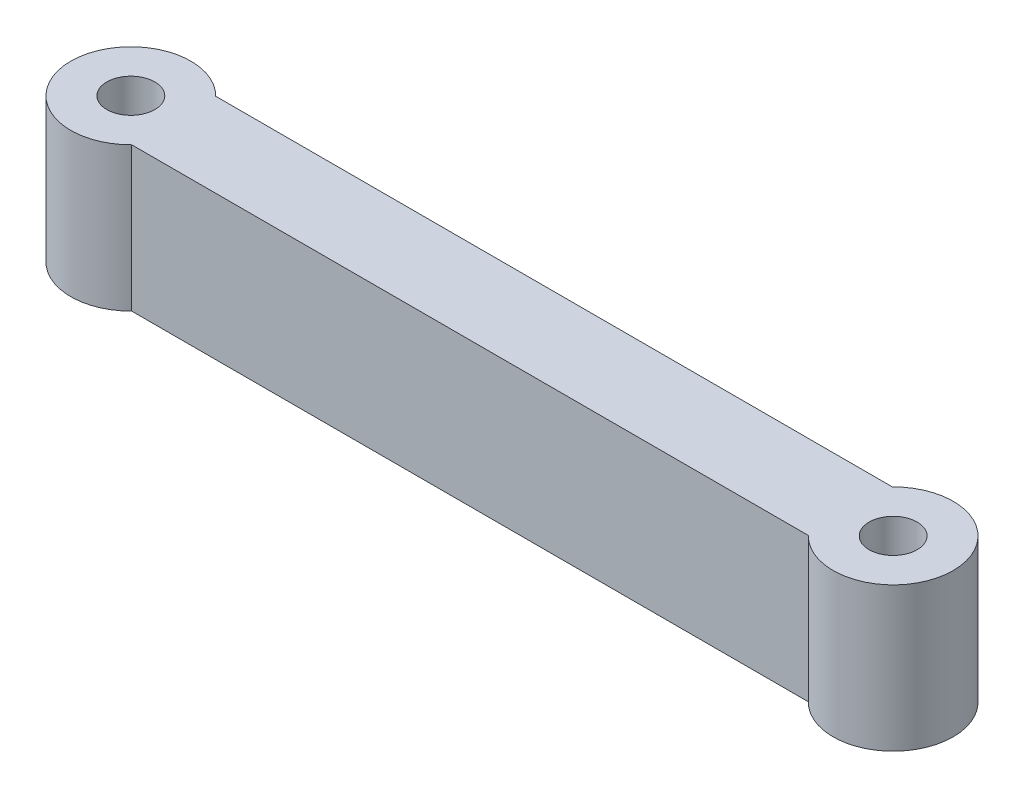
SolidWorks part; units mm, degrees
ref_plane "Alzado" through (0, 0, 0) normal (0, 0, 1) x (1, 0, 0)
ref_plane "Planta" through (0, 0, 0) normal (0, 1, 0) x (1, 0, 0)
ref_plane "Vista lateral" through (0, 0, 0) normal (1, 0, 0) x (0, 0, -1)
sketch "Croquis1" plane through (0, 0, 0) normal (0, 1, 0) x (1, 0, 0)
  line L1 (-28, 2.5) -> (28, 2.5)
  line L2 (-28, 2.5) -> (-28, -2.5)
  line L3 (-28, -2.5) -> (28, -2.5)
  line L4 (28, 2.5) -> (28, -2.5)
  line L5 (-28, 2.5) -> (28, -2.5) construction
  line L6 (-28, -2.5) -> (28, 2.5) construction
  point P0 (0, 0)
  dimension "D1" = 5
  dimension "D2" = 56
extrude "Saliente-Extruir1" add sketch "Croquis1" along normal blind 12
sketch "Croquis2" plane through (0, 12, 0) normal (0, 1, 0) x (1, 0, 0)
  line L0 (-28, 2.5) -> (-28, -2.5) construction
  circle A0 centre (31.75, 0) radius 4
  circle A1 centre (-31.75, 0) radius 4
  dimension "D2" = 8
  dimension "D3" = 8
  dimension "D1" = 63.5
  dimension "D4" = 59.75
extrude "Saliente-Extruir2" add sketch "Croquis2" against normal blind 12
sketch "Croquis3" plane through (0, 12, 0) normal (0, 1, 0) x (1, 0, 0)
  line L1 (-30.5992, 2.75) -> (30.5992, 2.75)
  line L2 (-30.5992, 2.75) -> (-30.5992, -2.75)
  line L3 (-30.5992, -2.75) -> (30.5992, -2.75)
  line L4 (30.5992, 2.75) -> (30.5992, -2.75)
  line L5 (-30.5992, 2.75) -> (30.5992, -2.75) construction
  line L6 (-30.5992, -2.75) -> (30.5992, 2.75) construction
  point P0 (0, 0)
  dimension "D1" = 5.5
extrude "Saliente-Extruir3" add sketch "Croquis3" against normal blind 12
sketch "Croquis4" plane through (0, 12, 0) normal (0, 1, 0) x (1, 0, 0)
  circle A0 centre (-31.75, 0) radius 2
  circle A1 centre (31.75, 0) radius 2
  dimension "D1" = 4
  dimension "D2" = 4
  dimension "D3" = 63.5
extrude "Cortar-Extruir1" cut sketch "Croquis4" against normal blind 12
sketch "Croquis5" plane through (0, 12, 0) normal (0, 1, 0) x (1, 0, 0)
  circle A0 centre (-31.75, 0) radius 5
  circle A1 centre (31.75, 0) radius 5
  dimension "D1" = 10
  dimension "D2" = 10
extrude "Saliente-Extruir4" add sketch "Croquis5" against normal blind 12
sketch "Croquis6" plane through (0, 12, 0) normal (0, 1, 0) x (1, 0, 0)
  line L1 (-28.1793, 3.5) -> (28.1793, 3.5)
  line L2 (-28.1793, 3.5) -> (-28.1793, -3.5)
  line L3 (-28.1793, -3.5) -> (28.1793, -3.5)
  line L4 (28.1793, 3.5) -> (28.1793, -3.5)
  line L5 (-28.1793, 3.5) -> (28.1793, -3.5) construction
  line L6 (-28.1793, -3.5) -> (28.1793, 3.5) construction
  arc A0 (27.5742, -2.75) -> (27.5742, 2.75) centre (31.75, 0) ccw construction
  point P0 (0, 0)
  dimension "D1" = 7
extrude "Saliente-Extruir5" add sketch "Croquis6" against normal blind 12
sketch "Croquis7" plane through (0, 12, 0) normal (0, 1, 0) x (1, 0, 0)
  circle A0 centre (31.75, 0) radius 2
  circle A1 centre (-31.75, 0) radius 2
  dimension "D1" = 4
  dimension "D2" = 4
extrude "Cortar-Extruir2" cut sketch "Croquis7" against normal blind 12
